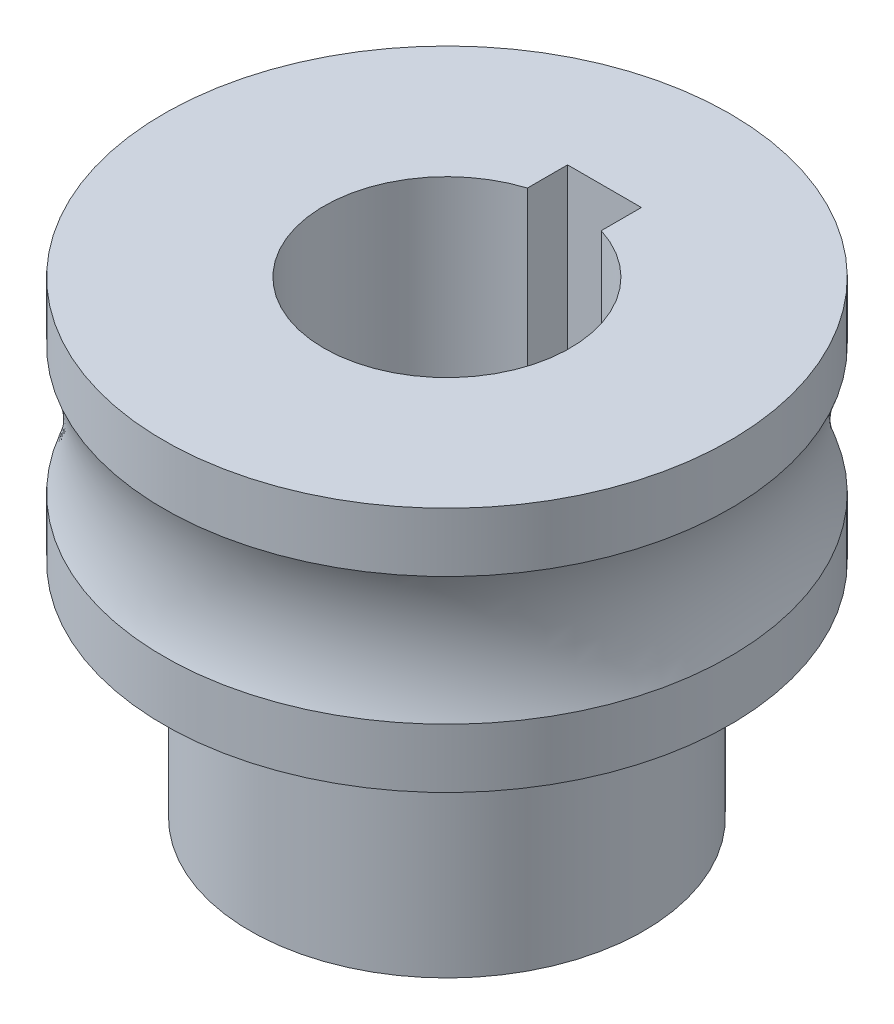
SolidWorks part; units mm, degrees
material "Laiton au plomb 2%, UNS C34200"
ref_plane "Plan de face" through (0, 0, 0) normal (0, 0, 1) x (1, 0, 0)
ref_plane "Plan de dessus" through (0, 0, 0) normal (0, 1, 0) x (1, 0, 0)
ref_plane "Plan de droite" through (0, 0, 0) normal (1, 0, 0) x (0, 0, -1)
sketch "Sketch1" plane through (0, 0, 0) normal (0, 0, 1) x (1, 0, 0)
  line L0 (5, -15) -> (8, -15)
  line L1 (8, -15) -> (8, -5)
  line L2 (8, -5) -> (11.5, -5)
  line L3 (11.5, -5) -> (11.5, -2.5981)
  line L4 (11.5, 5) -> (5, 5)
  line L5 (5, 5) -> (5, -15)
  line L6 (0, -15) -> (0, 19.6952) construction
  line L7 (11.5, 2.5981) -> (11.5, 5)
  line L8 (8, -5) -> (5, -5)
  arc A1 (11.5, 2.5981) -> (11.5, -2.5981) centre (18, 0) ccw
  point P10 (5, 0)
  dimension "D6" = 18
  dimension "D7" = 14
  dimension "D1" = 10
  dimension "D2" = 20
  dimension "D3" = 8
  dimension "D4" = 10
  dimension "D5" = 11.5
  dimension "D8" = 5
revolve "Revolve2" add sketch "Sketch1" angle 360 about L6
ref_plane "Plane1" through (0, 0, 0) normal (0, 1, 0) x (1, 0, 0)
sketch "Esquisse1" plane through (0, 5, 0) normal (0, 1, 0) x (1, 0, 0)
  line L1 (-1.5, 3.6) -> (1.5, 3.6)
  line L2 (-1.5, 3.6) -> (-1.5, 6.4)
  line L3 (-1.5, 6.4) -> (1.5, 6.4)
  line L4 (1.5, 3.6) -> (1.5, 6.4)
  line L5 (-1.5, 3.6) -> (1.5, 6.4) construction
  line L6 (-1.5, 6.4) -> (1.5, 3.6) construction
  circle A0 centre (0, 0) radius 5 construction
  point P0 (0, 5)
  dimension "D1" = 3
  dimension "D2" = 1.4
extrude "Enlèv. mat.-Extru.1" cut sketch "Esquisse1" against normal through all
sketch "Esquisse2" plane through (0, -15, 0) normal (0, -1, 0) x (1, 0, 0)
  circle A0 centre (0, 0) radius 8
  dimension "D1" = 16
extrude "Enlèv. mat.-Extru.2" cut sketch "Esquisse2" against normal blind 1
